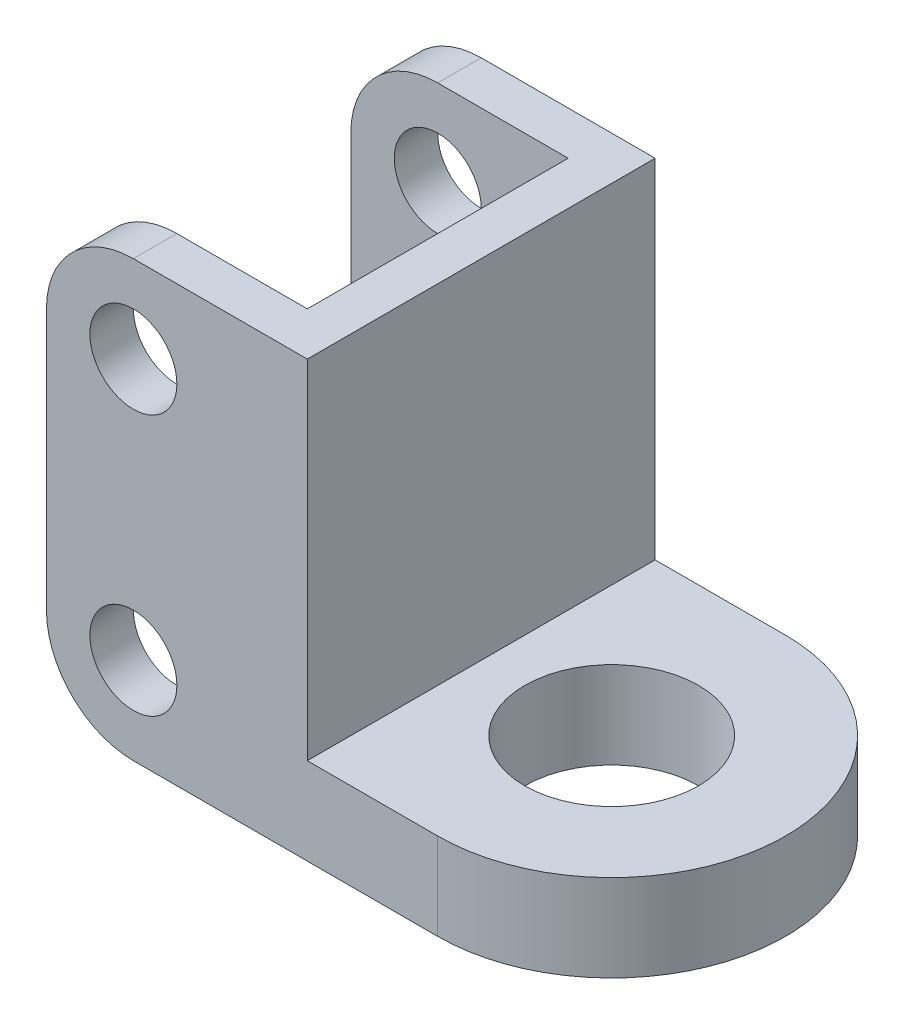
SolidWorks part; units mm, degrees
ref_plane "Front Plane" through (0, 0, 0) normal (0, 0, 1) x (1, 0, 0)
ref_plane "Top Plane" through (0, 0, 0) normal (0, 1, 0) x (1, 0, 0)
ref_plane "Right Plane" through (0, 0, 0) normal (1, 0, 0) x (0, 0, -1)
sketch "Sketch1" plane through (0, 0, 0) normal (0, 1, 0) x (1, 0, 0)
  line L0 (-22.5, 15) -> (2.5, 15)
  line L1 (-22.5, 20) -> (22.5, 20)
  line L2 (-22.5, 20) -> (-22.5, 15)
  line L3 (-22.5, -20) -> (22.5, -20)
  line L5 (2.5, 15) -> (2.5, -15)
  line L6 (2.5, -15) -> (-22.5, -15)
  line L7 (42.5, 0) -> (42.9677, 0) construction
  line L8 (-22.5, -15) -> (-22.5, -20)
  arc A1 (22.5, -20) -> (22.5, 20) centre (22.5, 0) ccw
  circle A2 centre (22.5, 0) radius 10
  point P0 (0, 0)
  dimension "D2" = 20
  dimension "D1" = 45
  dimension "D3" = 40
  dimension "D4" = 5
  dimension "D5" = 5
  dimension "D6" = 25
extrude "Boss-Extrude1" add sketch "Sketch1" along normal blind 10
sketch "Sketch2" plane through (0, 0, -20) normal (0, 0, -1) x (-1, 0, 0)
  line L0 (22.5, 0) -> (22.5, 50)
  line L1 (22.5, 50) -> (-2.5, 50)
  line L2 (-2.5, 50) -> (-2.5, 0)
  line L3 (22.5, 0) -> (-22.5, 0) construction
  line L4 (-2.5, 0) -> (22.5, 0)
  line L5 (22.5, 10) -> (-22.5, 10) construction
  dimension "D1" = 25
  dimension "D2" = 40
extrude "Boss-Extrude2" add sketch "Sketch2" against normal blind 5
sketch "Sketch3" plane through (0, 0, 20) normal (0, 0, 1) x (1, 0, 0)
  line L1 (-22.5, 50) -> (2.5, 50)
  line L2 (-22.5, 50) -> (-22.5, 0)
  line L3 (-22.5, 0) -> (2.5, 0)
  line L4 (2.5, 50) -> (2.5, 0)
extrude "Boss-Extrude3" add sketch "Sketch3" against normal blind 5
sketch "Sketch4" plane through (0, 0, 20) normal (0, 0, 1) x (1, 0, 0)
  line L0 (2.5, 10) -> (22.5, 10) construction
  line L1 (2.5, 50) -> (7.5, 50)
  line L2 (2.5, 50) -> (2.5, 10)
  line L3 (2.5, 10) -> (7.5, 10)
  line L4 (7.5, 50) -> (7.5, 10)
  dimension "D1" = 5
extrude "Boss-Extrude4" add sketch "Sketch4" against normal up to surface (40 mm away) up to face at (0.8333, 20, -20)
sketch "Sketch5" plane through (0, 0, 20) normal (0, 0, 1) x (1, 0, 0)
  line L0 (-12.5, 63.8171) -> (-12.5, -17.6509) construction
  line L1 (-12.5, 15) -> (-40.3364, 15) construction
  line L2 (-12.5, 35) -> (-43.4912, 35) construction
  line L3 (-42.1922, 40) -> (23.1306, 40) construction
  line L4 (-17.5, 40) -> (-17.5, 72.9103) construction
  line L5 (-22.5, 50) -> (-22.5, 0) construction
  line L6 (-12.5, 45) -> (-30.7745, 45) construction
  line L7 (-12.5, 5) -> (-30.7745, 5) construction
  line L8 (-22.5, 0) -> (22.5, 0) construction
  line L9 (7.5, 50) -> (-22.5, 50) construction
  circle A0 centre (-12.5, 40) radius 5
  circle A1 centre (-12.5, 10) radius 5
  dimension "D1" = 10
  dimension "D2" = 10
  dimension "D3" = 20
  dimension "D4" = 5
  dimension "D5" = 5
  dimension "D6" = 5
extrude "Cut-Extrude1" cut sketch "Sketch5" against normal through all both and the other way through all
fillet "Fillet1" radius 10 4 edges at (-22.5, 50, 17.5) (-22.5, 0, -17.5) (-22.5, 50, -17.5) (-22.5, 0, 17.5)
